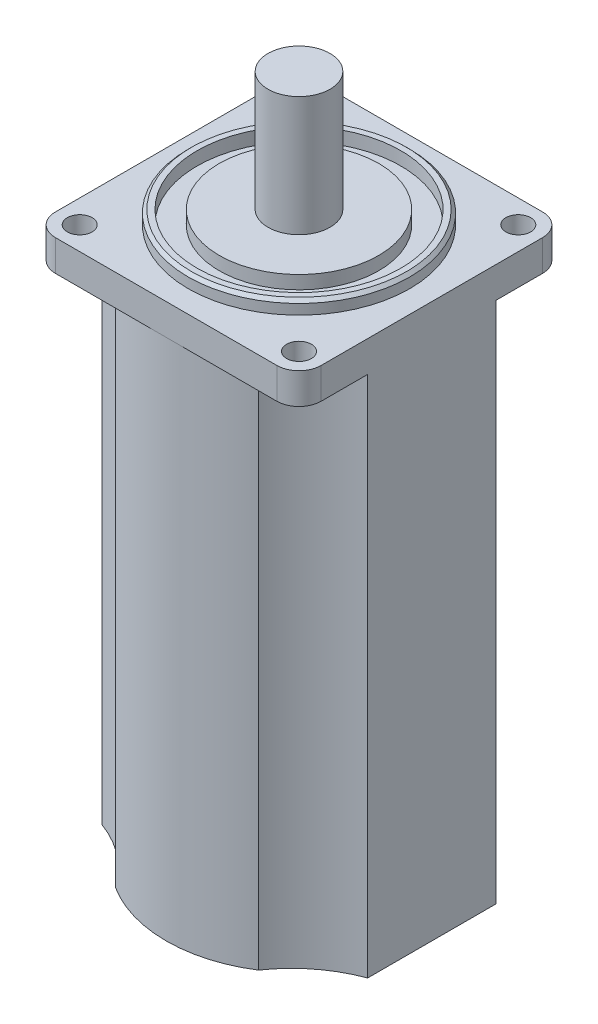
SolidWorks part; units mm, degrees
ref_plane "Front Plane" through (0, 0, 0) normal (0, 0, 1) x (1, 0, 0)
ref_plane "Top Plane" through (0, 0, 0) normal (0, 1, 0) x (1, 0, 0)
ref_plane "Right Plane" through (0, 0, 0) normal (1, 0, 0) x (0, 0, -1)
sketch "Sketch1" plane through (0, 0, 0) normal (0, 1, 0) x (1, 0, 0)
  line L0 (0, 0) -> (0, 55.1168) construction
  line L1 (-25, -30) -> (25, -30)
  line L2 (-30, -25) -> (-30, 25)
  line L3 (-25, 30) -> (25, 30)
  line L4 (30, -25) -> (30, 25)
  line L5 (-30, -30) -> (30, 30) construction
  line L6 (-30, 30) -> (30, -30) construction
  line L7 (0, 0) -> (57.8565, 0) construction
  arc A0 (-25, -30) -> (-30, -25) centre (-25, -25) cw
  arc A1 (25, -30) -> (30, -25) centre (25, -25) ccw
  arc A2 (25, 30) -> (30, 25) centre (25, 25) cw
  arc A3 (-30, 25) -> (-25, 30) centre (-25, 25) cw
  circle A4 centre (-24.7487, 24.7487) radius 2.8
  circle A5 centre (24.7487, 24.7487) radius 2.8
  circle A6 centre (24.7487, -24.7487) radius 2.8
  circle A7 centre (-24.7487, -24.7487) radius 2.8
  point P0 (0, 0)
  dimension "D2" = 5
  dimension "D3" = 5.6
  dimension "D4" = 70
  dimension "D1" = 60
extrude "Boss-Extrude1" add sketch "Sketch1" along normal blind 7
sketch "Sketch2" plane through (0, 7, 0) normal (0, 1, 0) x (1, 0, 0)
  circle A0 centre (0, 0) radius 25
  circle A1 centre (0, 0) radius 23
  circle A2 centre (0, 0) radius 18
  dimension "D1" = 50
  dimension "D3" = 36
  dimension "D2" = 2
extrude "Boss-Extrude3" add sketch "Sketch2" along normal blind 3
chamfer "Chamfer2" distance 0.71 angle 45 1 edges at (0, 10, 25)
sketch "Sketch3" plane through (0, 0, 0) normal (0, -1, 0) x (1, 0, 0)
  line L0 (-25, 30) -> (25, 30) construction
  line L3 (0, 0) -> (0, 42.3757) construction
  line L4 (0, 0) -> (47.0049, 0) construction
  line L6 (-30, 14.5) -> (-30, -14.5)
  line L7 (30, 14.5) -> (30, -14.5)
  arc A0 (16.12, 25.3011) -> (-16.12, 25.3011) centre (0, 0) ccw
  arc A1 (-16.12, 25.3011) -> (-30, 14.5) centre (-40.0314, 41.7098) cw
  arc A2 (16.12, 25.3011) -> (30, 14.5) centre (40.0314, 41.7098) ccw
  arc A3 (-16.12, -25.3011) -> (-30, -14.5) centre (-40.0314, -41.7098) ccw
  arc A4 (16.12, -25.3011) -> (-16.12, -25.3011) centre (0, 0) cw
  arc A5 (16.12, -25.3011) -> (30, -14.5) centre (40.0314, -41.7098) cw
  point P4 (0, 30)
  point P7 (0, 30)
  dimension "D1" = 30
  dimension "D4" = 29
  dimension "D2" = 32.24
  dimension "D3" = 29
extrude "Boss-Extrude4" add sketch "Sketch3" along normal blind 118
sketch "Sketch4" plane through (0, 7, 0) normal (0, 1, 0) x (1, 0, 0)
  circle A1 centre (0, 0) radius 23
  circle A3 centre (0, 0) radius 23
  dimension "D1" = 0
sketch "Sketch5" plane through (0, 10, 0) normal (0, 1, 0) x (1, 0, 0)
  circle A0 centre (0, 0) radius 7
  dimension "D1" = 14
extrude "Boss-Extrude5" add sketch "Sketch5" along normal blind 27
